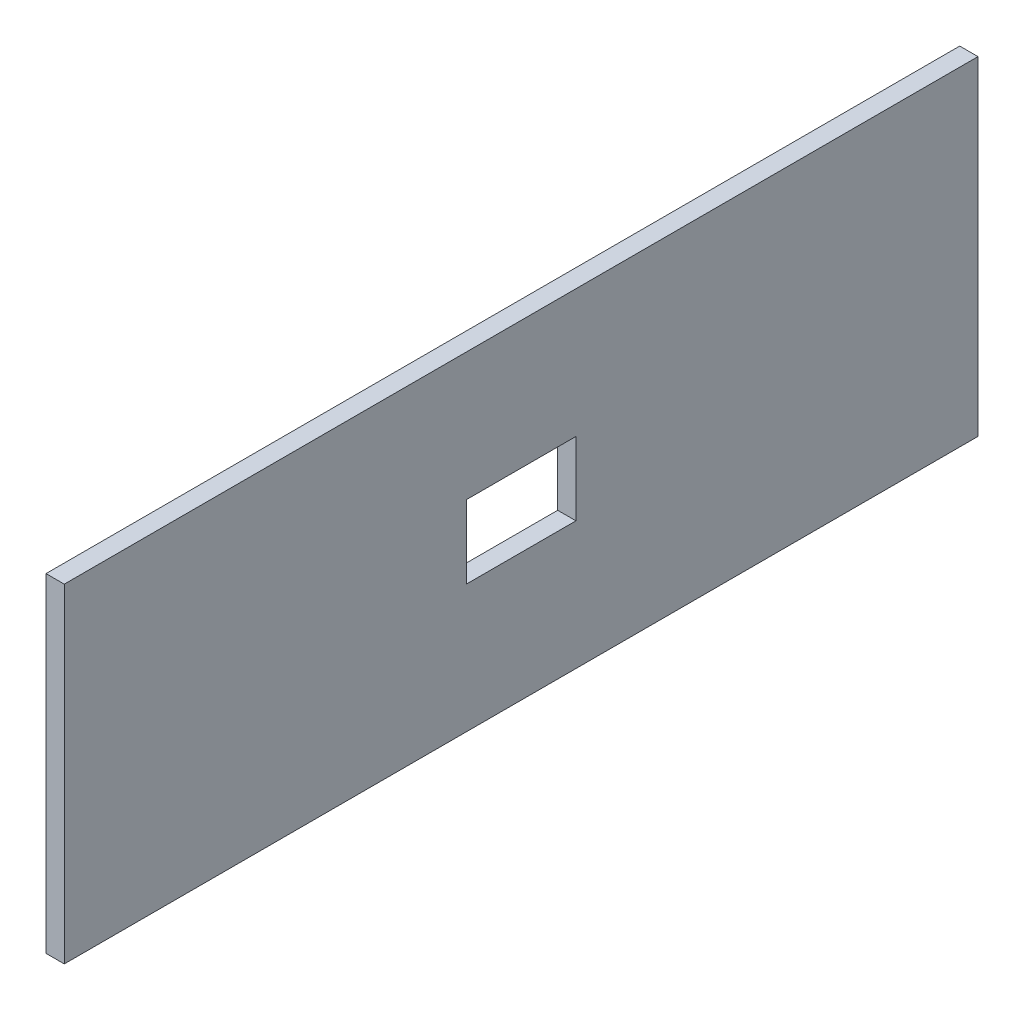
SolidWorks part; units mm, degrees
ref_plane "Front Plane" through (0, 0, 0) normal (0, 0, 1) x (1, 0, 0)
ref_plane "Top Plane" through (0, 0, 0) normal (0, 1, 0) x (1, 0, 0)
ref_plane "Right Plane" through (0, 0, 0) normal (1, 0, 0) x (0, 0, -1)
sketch "Sketch1" plane through (0, 0, 0) normal (1, 0, 0) x (0, 0, -1)
  line L1 (-125, 45) -> (125, 45)
  line L2 (-125, 45) -> (-125, -45)
  line L3 (-125, -45) -> (125, -45)
  line L4 (125, 45) -> (125, -45)
  line L5 (-125, 45) -> (125, -45) construction
  line L6 (-125, -45) -> (125, 45) construction
  point P0 (0, 0)
  dimension "D1" = 250
  dimension "D2" = 90
extrude "Boss-Extrude1" add sketch "Sketch1" along normal blind 5
sketch "Sketch2" plane through (5, 0, 0) normal (1, 0, 0) x (0, 0, -1)
  line L1 (-15, 10) -> (15, 10)
  line L2 (-15, 10) -> (-15, -10)
  line L3 (-15, -10) -> (15, -10)
  line L4 (15, 10) -> (15, -10)
  line L5 (-15, 10) -> (15, -10) construction
  line L6 (-15, -10) -> (15, 10) construction
  point P0 (0, 0)
  dimension "D1" = 30
  dimension "D2" = 20
extrude "Cut-Extrude1" cut sketch "Sketch2" against normal blind 10
